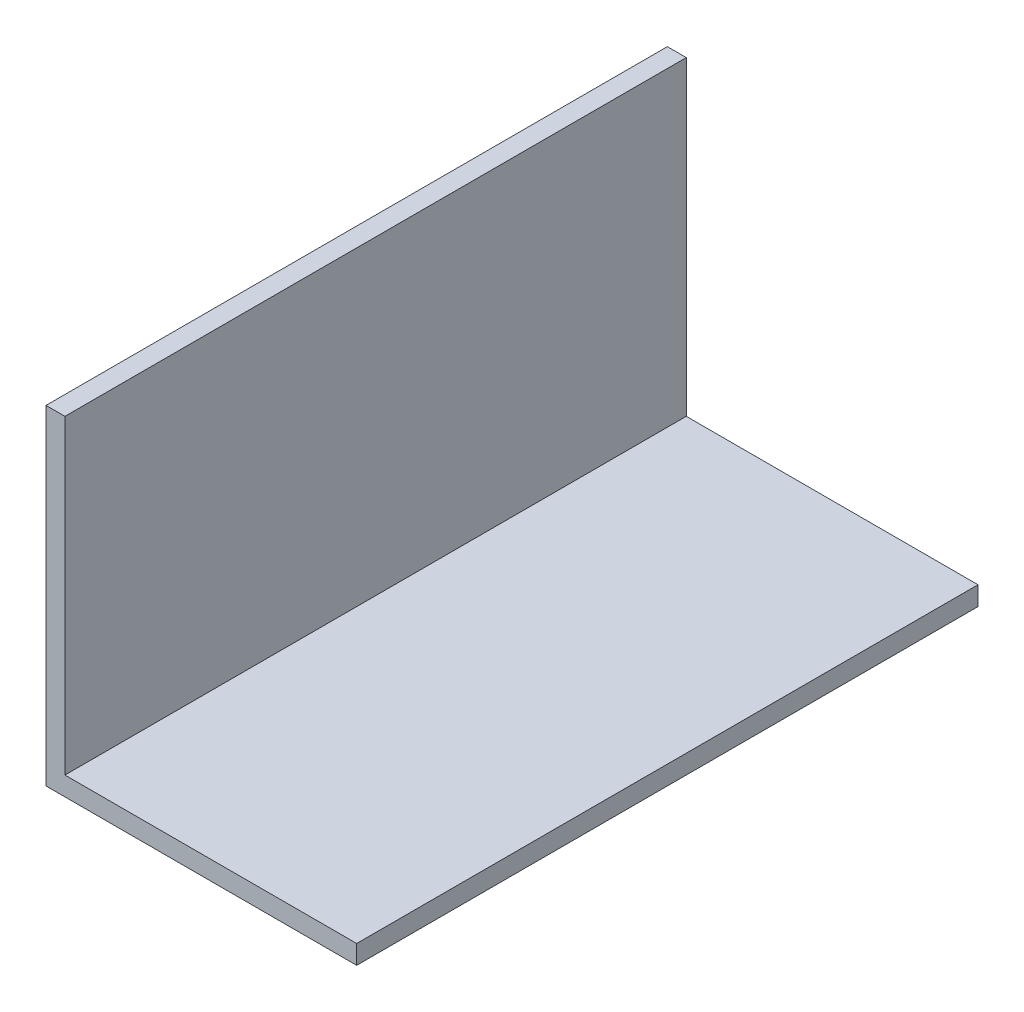
SolidWorks part; units mm, degrees
ref_plane "Plan de face" through (0, 0, 0) normal (0, 0, 1) x (1, 0, 0)
ref_plane "Plan de dessus" through (0, 0, 0) normal (0, 1, 0) x (1, 0, 0)
ref_plane "Plan de droite" through (0, 0, 0) normal (1, 0, 0) x (0, 0, -1)
sketch "wall" plane through (0, 0, 0) normal (0, 0, 1) x (1, 0, 0)
  line L0 (0, 0) -> (0, 5304.8)
  line L1 (0, 5304.8) -> (304.8, 5304.8)
  line L2 (304.8, 5304.8) -> (304.8, 304.8)
  line L3 (304.8, 304.8) -> (5000, 304.8)
  line L4 (5000, 304.8) -> (5000, 0)
  line L5 (5000, 0) -> (0, 0)
  dimension "D1" = 304.8
  dimension "D2" = 5000
  dimension "D3" = 304.8
  dimension "D4" = 5000
extrude "Boss-Extrude1" add sketch "wall" along normal blind 5000 and the other way blind 4999.99
equation "\"wall thickness\"= 1ft"
equation "\"D1@wall\" = \"wall thickness\""
equation "\"lagoon depth\"= 5m"
equation "\"D2@wall\" = \"lagoon depth\""
equation "\"D3@wall\" = \"wall thickness\""
equation "\"D4@wall\" = \"lagoon depth\""
equation "\"D1@Boss-Extrude1\"=\"lagoon depth\""
